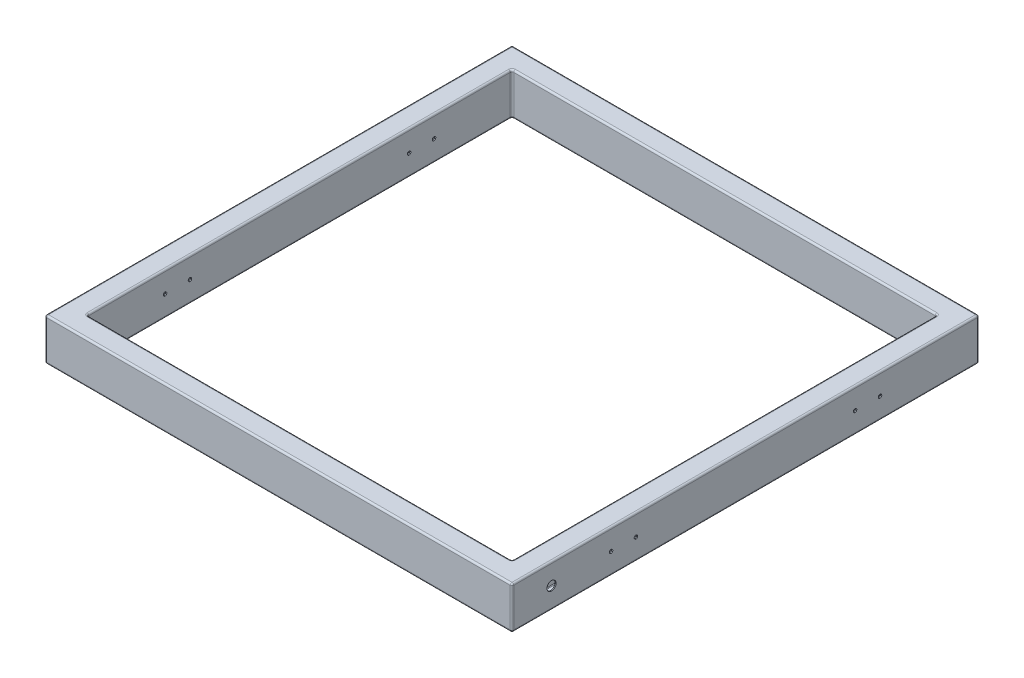
SolidWorks part; units mm, degrees
material "Plain Carbon Steel"
ref_plane "Front" through (0, 0, 0) normal (0, 0, 1) x (1, 0, 0)
ref_plane "Top" through (0, 0, 0) normal (0, 1, 0) x (1, 0, 0)
ref_plane "Right" through (0, 0, 0) normal (1, 0, 0) x (0, 0, -1)
sketch "Sketch1" plane through (0, 0, 0) normal (0, 1, 0) x (1, 0, 0)
  line L1 (-665, 665) -> (665, 665)
  line L2 (-665, 665) -> (-665, -665)
  line L3 (-665, -665) -> (665, -665)
  line L4 (665, 665) -> (665, -665)
  line L5 (-665, 665) -> (665, -665) construction
  line L6 (-665, -665) -> (665, 665) construction
  line L7 (-605, 605) -> (605, 605)
  line L8 (-605, 605) -> (-605, -605)
  line L9 (-605, -605) -> (605, -605)
  line L10 (605, 605) -> (605, -605)
  line L11 (-605, 605) -> (605, -605) construction
  line L12 (-605, -605) -> (605, 605) construction
  point P0 (0, 0)
  point P6 (0, 0)
  dimension "D1" = 1330
  dimension "D2" = 60
extrude "Boss-Extrude1" add sketch "Sketch1" along normal blind 120
fillet "Fillet1" radius 5 24 edges at (-665, 60, 665) (665, 60, 665) (0, 0, 665) (0, 120, 665) (-665, 120, 0) (0, 120, -665) (665, 120, 0) (-605, 120, 0) (0, 120, 605) (605, 120, 0) (0, 120, -605) (665, 60, -665) (-665, 60, -665) (-665, 0, 0) (0, 0, -665) (665, 0, 0) (605, 60, -605) (-605, 60, -605) (-605, 60, 605) (605, 60, 605) (0, 0, 605) (-605, 0, 0) (0, 0, -605) (605, 0, 0)
shell "Shell1" thickness 3
sketch "Sketch2" plane through (-665, 0, 0) normal (-1, 0, 0) x (0, 0, 1)
  circle A0 centre (-383, 60) radius 5
  circle A1 centre (-312, 60) radius 5
  circle A2 centre (383, 60) radius 5
  circle A3 centre (312, 60) radius 5
  dimension "D1" = 10
extrude "Cut-Extrude1" cut sketch "Sketch2" against normal through all
sketch "Sketch3" plane through (665, 0, 0) normal (1, 0, 0) x (0, 0, -1)
  line L0 (-500, 60) -> (-605, 60) construction
  line L1 (-500, -420) -> (-500, 1214) construction
  line L2 (-605, -360.5) -> (-605, -239.5) construction
  line L3 (-660, 120) -> (660, 120) construction
  circle A0 centre (-552.5, 60) radius 13
  dimension "D2" = 26
  dimension "D1" = 60
extrude "Cut-Extrude2" cut sketch "Sketch3" against normal up to surface (60 mm away) up to face at (605, 60, -378)
